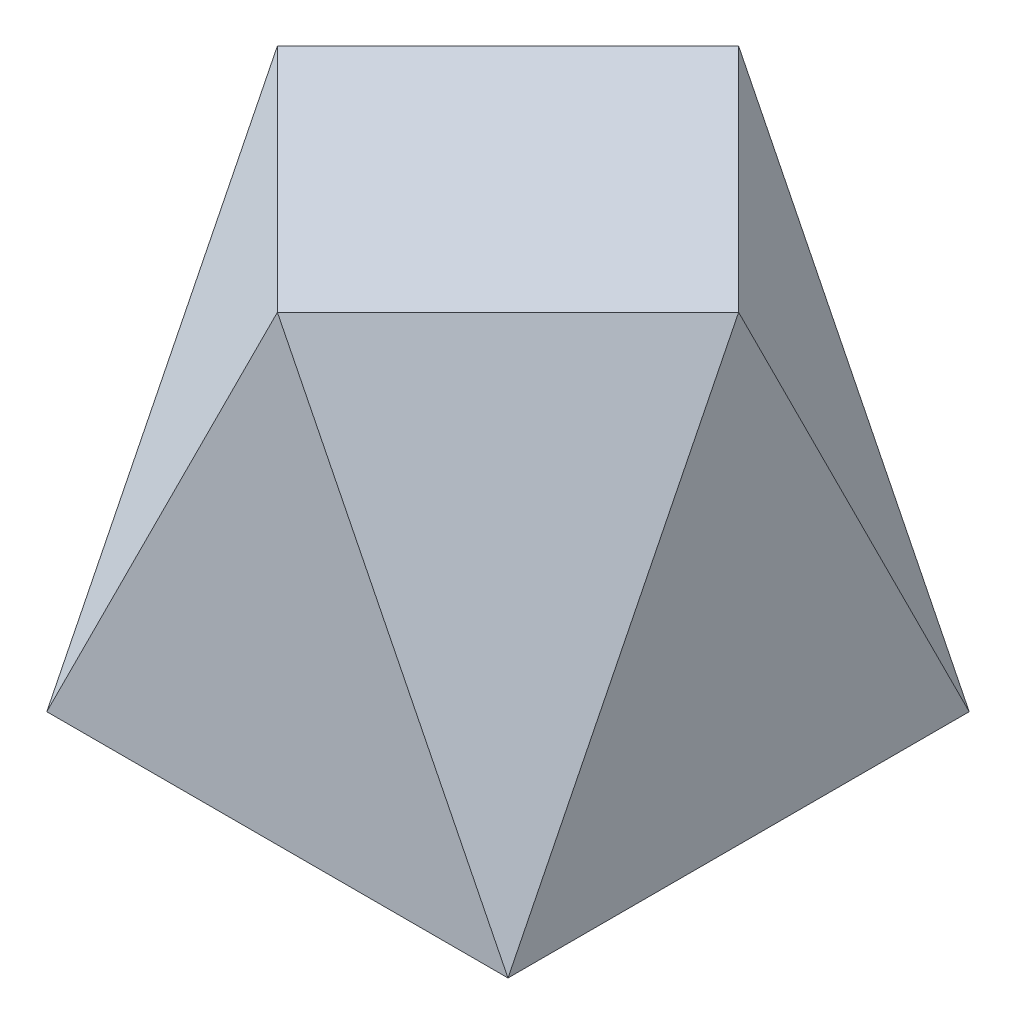
SolidWorks part; units mm, degrees
ref_plane "Front" through (0, 0, 0) normal (0, 0, 1) x (1, 0, 0)
ref_plane "Top" through (0, 0, 0) normal (0, 1, 0) x (1, 0, 0)
ref_plane "Right" through (0, 0, 0) normal (1, 0, 0) x (0, 0, -1)
sketch "Sketch1" plane through (0, 0, 0) normal (0, 1, 0) x (1, 0, 0)
  line L1 (-2, -2) -> (2, -2)
  line L2 (-2, -2) -> (-2, 2)
  line L3 (-2, 2) -> (2, 2)
  line L4 (2, -2) -> (2, 2)
  line L5 (-2, -2) -> (2, 2) construction
  line L6 (-2, 2) -> (2, -2) construction
  point P0 (0, 0)
  dimension "D1" = 4
  dimension "D2" = 4
extrude "Boss-Extrude1" add sketch "Sketch1" along normal blind 4
sketch3d "3DSketch1"
  line L0 (-2, 0, 2) -> (0, 4, 2)
  line L1 (-2, 4, 2) -> (2, 4, 2) construction
  line L2 (0, 4, 2) -> (-2, 4, 0)
  line L3 (-2, 4, -2) -> (-2, 4, 2) construction
  line L4 (-2, 4, 0) -> (-2, 0, 2)
extrude "Cut-Extrude1" cut sketch "3DSketch1" along direction (1, 0, 0) on the side of the normal blind 4
sketch3d "3DSketch2"
  line L0 (0, 4, 2) -> (2, 0, 2)
  line L1 (2, 0, 2) -> (2, 4, 0)
  line L2 (2, 4, 2) -> (2, 4, -2) construction
  line L3 (2, 4, 0) -> (-0.446, 1.554, 0)
  line L4 (0, 4, 2) -> (2, 4, 0)
extrude "Cut-Extrude3" cut sketch "3DSketch2" along direction (-1, 0, 0) on the side of the normal blind 4 contours L1 L4 L0
sketch3d "3DSketch3"
  line L0 (2, 0, -2) -> (2, 4, 0)
  line L3 (2, 4, 0) -> (0, 4, -2)
  line L4 (2, 4, -2) -> (-2, 4, -2) construction
  line L5 (0, 4, -2) -> (2, 0, -2)
extrude "Cut-Extrude5" cut sketch "3DSketch3" along direction (0, 0, 1) on the side against the normal blind 4
sketch3d "3DSketch4"
  line L0 (0, 4, -2) -> (-2, 0.078, -2)
  line L1 (-2, 4, -2) -> (-2, 0, -2) construction
  line L2 (-2, 0.078, -2) -> (-2, 4, 0)
  line L3 (-2, 4, 0) -> (0, 4, -2)
extrude "Cut-Extrude6" cut sketch "3DSketch4" along direction (1, 0, 0) on the side of the normal blind 4
